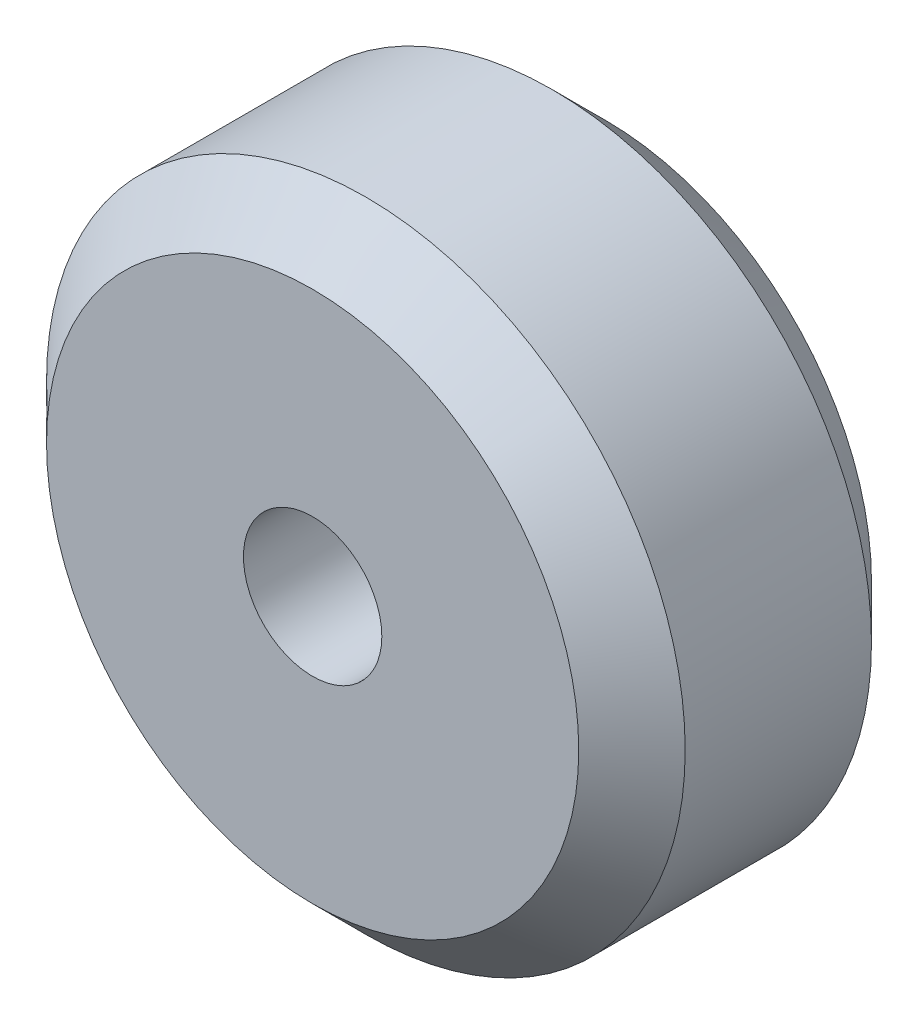
SolidWorks part; units mm, degrees
ref_plane "Front Plane" through (0, 0, 0) normal (0, 0, 1) x (1, 0, 0)
ref_plane "Top Plane" through (0, 0, 0) normal (0, 1, 0) x (1, 0, 0)
ref_plane "Right Plane" through (0, 0, 0) normal (1, 0, 0) x (0, 0, -1)
sketch "Sketch1" plane through (0, 0, 0) normal (0, 0, 1) x (1, 0, 0)
  circle A0 centre (0, 0) radius 12
  dimension "D1" = 24
extrude "Boss-Extrude1" add sketch "Sketch1" along normal blind 11
chamfer "Chamfer1" distance 2 angle 45 2 edges at (12, 0, 0) (12, 0, 11)
sketch "Sketch2" plane through (0, 0, 11) normal (0, 0, 1) x (1, 0, 0)
  circle A0 centre (0, 0) radius 2.6
  dimension "D1" = 5.2
extrude "Cut-Extrude1" cut sketch "Sketch2" against normal up to surface (11 mm away) up to face at (10, 0, 0)
